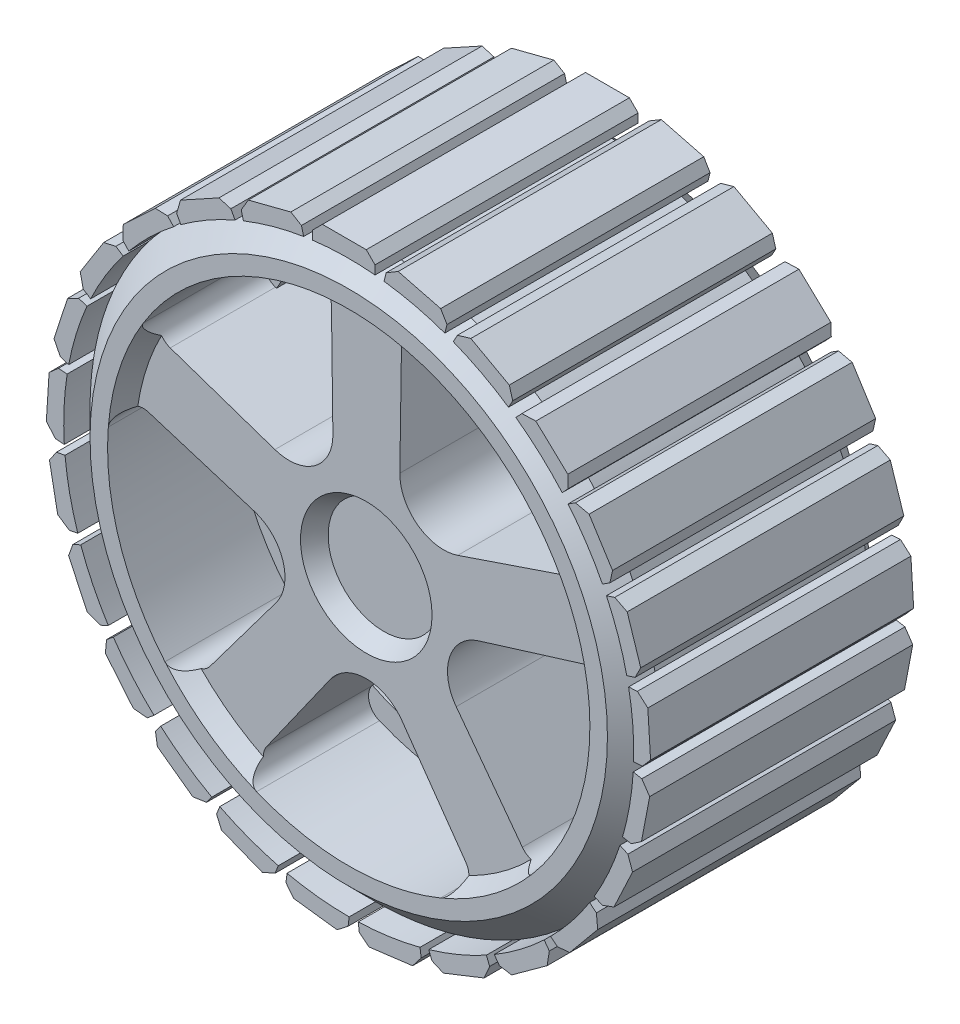
SolidWorks part; units mm, degrees
ref_plane "Front Plane" through (0, 0, 0) normal (0, 0, 1) x (1, 0, 0)
ref_plane "Top Plane" through (0, 0, 0) normal (0, 1, 0) x (1, 0, 0)
ref_plane "Right Plane" through (0, 0, 0) normal (1, 0, 0) x (0, 0, -1)
sketch "Sketch1" plane through (0, 0, 0) normal (0, 0, 1) x (1, 0, 0)
  circle A0 centre (0, 0) radius 32.5
  dimension "D1" = 65
extrude "Boss-Extrude1" add sketch "Sketch1" along normal mid plane 30
sketch "Sketch3" plane through (0, 0, 15) normal (0, 0, 1) x (1, 0, 0)
  line L0 (-24.6182, 12.2553) -> (-10.4207, 7.4109)
  line L1 (-3.8065, 12.2075) -> (-4, 27.2075)
  line L2 (0, 0) -> (0, 89.3086) construction
  line L3 (4.048, 27.2004) -> (3.828, 12.2008)
  line L4 (10.4338, 7.3925) -> (24.6398, 12.2118)
  line L5 (27.1201, 4.5555) -> (12.7866, 0.1296)
  line L6 (10.2549, -7.6387) -> (19.2283, -19.6602)
  line L7 (12.7131, -24.385) -> (4.0745, -12.1207)
  line L8 (-4.0959, -12.1135) -> (-12.7561, -24.3625)
  line L9 (-19.2629, -19.6262) -> (-10.2684, -7.6206)
  line L10 (-12.7863, 0.1522) -> (-27.112, 4.6034)
  circle A1 centre (0, 0) radius 27.5
  arc A2 (-10.4207, 7.4109) -> (-3.8065, 12.2075) centre (-8.8061, 12.143) ccw
  arc A3 (-4, 27.2075) -> (-24.6182, 12.2553) centre (0, 0) ccw
  circle A4 centre (0, 0) radius 10 construction
  arc A5 (24.6398, 12.2118) -> (4.048, 27.2004) centre (0, 0) ccw
  arc A6 (3.828, 12.2008) -> (10.4338, 7.3925) centre (8.8275, 12.1275) ccw
  arc A7 (19.2283, -19.6602) -> (27.1201, 4.5555) centre (0, 0) ccw
  arc A8 (12.7866, 0.1296) -> (10.2549, -7.6387) centre (14.2618, -4.6478) ccw
  arc A9 (-12.7561, -24.3625) -> (12.7131, -24.385) centre (0, 0) ccw
  arc A10 (4.0745, -12.1207) -> (-4.0959, -12.1135) centre (-0.0132, -15) ccw
  arc A11 (-27.112, 4.6034) -> (-19.2629, -19.6262) centre (0, 0) ccw
  arc A12 (-10.2684, -7.6206) -> (-12.7863, 0.1522) centre (-14.2699, -4.6227) ccw
  point P35 (0, 0)
  dimension "D1" = 55
  dimension "D2" = 5
  dimension "D6" = 20
  dimension "D3" = 15
  dimension "D4" = 8
  dimension "D5" = 5
extrude "Cut-Extrude1" cut sketch "Sketch3" against normal through all contours L0 A2 L1 A1 | L9 A12 L10 A1 | L7 A10 L8 A1 | L5 A8 L6 A1 | L3 A6 L4 A1
fillet "Fillet1" radius 2 10 edges at (4.048, 27.2004, 0) (24.6398, 12.2118, 0) (27.1201, 4.5555, 0) (19.2283, -19.6602, 0) (12.7131, -24.385, 0) (-12.7561, -24.3625, 0) (-19.2629, -19.6262, 0) (-27.112, 4.6034, 0) (-24.6182, 12.2553, 0) (-4, 27.2075, 0)
sketch "Sketch5" plane through (0, 0, 15) normal (0, 0, 1) x (1, 0, 0)
  circle A0 centre (0, 0) radius 27.5
  dimension "D1" = 55
extrude "Cut-Extrude2" cut sketch "Sketch5" against normal blind 2 draft 30
sketch "Sketch7" plane through (0, 0, 13) normal (0, 0, 1) x (1, 0, 0)
  circle A0 centre (0, 0) radius 7.5
  point P2 (0, 0)
  dimension "D1" = 15
extrude "Cut-Extrude3" cut sketch "Sketch7" against normal blind 2 draft 30
mirror "Mirror1" about plane through (0, 0, 0) normal (0, 0, 1) of "Cut-Extrude3", "Cut-Extrude2"
chamfer "Chamfer1" distance 3 angle 45 2 edges at (32.5, 0, -15) (32.5, 0, 15)
sketch "Sketch9" plane through (0, 0, 0) normal (0, 0, 1) x (1, 0, 0)
  circle A16 centre (0, 0) radius 25
  circle A17 centre (0, 0) radius 30
  dimension "D1" = 50
  dimension "D2" = 5
extrude "Boss-Extrude2" add sketch "Sketch9" along normal mid plane 2
sketch "Sketch10" plane through (0, 0, 0) normal (0, 0, 1) x (1, 0, 0)
  line L0 (-4.1239, 32.2373) -> (-4.1239, 33.2373)
  line L1 (-3, 34.3612) -> (2, 34.3612)
  line L2 (3, 33.3612) -> (3, 32.3612)
  line L3 (0, 0) -> (0, -50000) construction
  line L4 (3, 33.3612) -> (2, 34.3612)
  line L5 (-4.1239, 33.2373) -> (-3, 34.3612)
  line L6 (4.0227, 32.2501) -> (4.2714, 33.2187)
  line L7 (4.2714, 33.2187) -> (5.6395, 34.0278)
  line L8 (5.6395, 34.0278) -> (10.4825, 32.7843)
  line L9 (11.2024, 31.5671) -> (10.4825, 32.7843)
  line L10 (11.2024, 31.5671) -> (10.9537, 30.5985)
  line L11 (11.9166, 30.2365) -> (12.3983, 31.1128)
  line L12 (12.3983, 31.1128) -> (13.9247, 31.5562)
  line L13 (13.9247, 31.5562) -> (18.3063, 29.1475)
  line L14 (18.7008, 27.7894) -> (18.3063, 29.1475)
  line L15 (18.7008, 27.7894) -> (18.2191, 26.9131)
  line L16 (19.0617, 26.323) -> (19.7463, 27.052)
  line L17 (19.7463, 27.052) -> (21.335, 27.1019)
  line L18 (21.335, 27.1019) -> (24.9798, 23.6792)
  line L19 (25.0242, 22.2657) -> (24.9798, 23.6792)
  line L20 (25.0242, 22.2657) -> (24.3397, 21.5367)
  line L21 (25.0091, 20.7556) -> (25.8535, 21.2914)
  line L22 (25.8535, 21.2914) -> (27.4047, 20.9447)
  line L23 (27.4047, 20.9447) -> (30.0838, 16.723)
  line L24 (29.7753, 15.3429) -> (30.0838, 16.723)
  line L25 (29.7753, 15.3429) -> (28.931, 14.807)
  line L26 (29.3851, 13.884) -> (30.3362, 14.193)
  line L27 (30.3362, 14.193) -> (31.7524, 13.4714)
  line L28 (31.7524, 13.4714) -> (33.2975, 8.7161)
  line L29 (32.6555, 7.456) -> (33.2975, 8.7161)
  line L30 (32.6555, 7.456) -> (31.7044, 7.147)
  line L31 (31.9147, 6.14) -> (32.9128, 6.2028)
  line L32 (32.9128, 6.2028) -> (34.1051, 5.1516)
  line L33 (34.1051, 5.1516) -> (34.419, 0.1615)
  line L34 (33.4838, -0.8993) -> (34.419, 0.1615)
  line L35 (33.4838, -0.8993) -> (32.4858, -0.9621)
  line L36 (32.439, -1.9898) -> (33.4213, -2.1771)
  line L37 (33.4213, -2.1771) -> (34.3148, -3.4918)
  line L38 (34.3148, -3.4918) -> (33.3778, -8.4032)
  line L39 (32.2082, -9.1981) -> (33.3778, -8.4032)
  line L40 (32.2082, -9.1981) -> (31.2259, -9.0108)
  line L41 (30.9251, -9.9945) -> (31.8299, -10.4203)
  line L42 (31.8299, -10.4203) -> (32.3683, -11.9158)
  line L43 (32.3683, -11.9158) -> (30.2394, -16.44)
  line L44 (28.9088, -16.919) -> (30.2394, -16.44)
  line L45 (28.9088, -16.919) -> (28.004, -16.4932)
  line L46 (27.468, -17.3713) -> (28.2385, -18.0087)
  line L47 (28.2385, -18.0087) -> (28.3881, -19.5911)
  line L48 (28.3881, -19.5911) -> (25.2009, -23.4437)
  line L49 (23.793, -23.5768) -> (25.2009, -23.4437)
  line L50 (23.793, -23.5768) -> (23.0225, -22.9394)
  line L51 (22.285, -23.6565) -> (22.8727, -24.4655)
  line L52 (22.8727, -24.4655) -> (22.6241, -26.0355)
  line L53 (22.6241, -26.0355) -> (18.579, -28.9744)
  line L54 (17.1822, -28.7532) -> (18.579, -28.9744)
  line L55 (17.1822, -28.7532) -> (16.5944, -27.9442)
  line L56 (15.7017, -28.4553) -> (16.0698, -29.3851)
  line L57 (16.0698, -29.3851) -> (15.4385, -30.8439)
  line L58 (15.4385, -30.8439) -> (10.7897, -32.6845)
  line L59 (9.4918, -32.1229) -> (10.7897, -32.6845)
  line L60 (9.4918, -32.1229) -> (9.1236, -31.1931)
  line L61 (8.1318, -31.4662) -> (8.2572, -32.4583)
  line L62 (8.2572, -32.4583) -> (7.2829, -33.7143)
  line L63 (7.2829, -33.7143) -> (2.3224, -34.341)
  line L64 (1.2049, -33.4742) -> (2.3224, -34.341)
  line L65 (1.2049, -33.4742) -> (1.0796, -32.4821)
  line L66 (0.051, -32.5) -> (-0.0743, -33.4921)
  line L67 (-0.0743, -33.4921) -> (-1.3303, -34.4663)
  line L68 (-1.3303, -34.4663) -> (-6.2908, -33.8396)
  line L69 (-7.1576, -32.7222) -> (-6.2908, -33.8396)
  line L70 (-7.1576, -32.7222) -> (-7.0323, -31.7301)
  line L71 (-8.033, -31.4916) -> (-8.4011, -32.4214)
  line L72 (-8.4011, -32.4214) -> (-9.8599, -33.0526)
  line L73 (-9.8599, -33.0526) -> (-14.5088, -31.212)
  line L74 (-15.0704, -29.9141) -> (-14.5088, -31.212)
  line L75 (-15.0704, -29.9141) -> (-14.7023, -28.9843)
  line L76 (-15.6123, -28.5045) -> (-16.2, -29.3135)
  line L77 (-16.2, -29.3135) -> (-17.77, -29.5622)
  line L78 (-17.77, -29.5622) -> (-21.8151, -26.6233)
  line L79 (-22.0363, -25.2265) -> (-21.8151, -26.6233)
  line L80 (-22.0363, -25.2265) -> (-21.4485, -24.4174)
  line L81 (-22.2106, -23.7264) -> (-22.9811, -24.3638)
  line L82 (-22.9811, -24.3638) -> (-24.5635, -24.2142)
  line L83 (-24.5635, -24.2142) -> (-27.7506, -20.3617)
  line L84 (-27.6176, -18.9537) -> (-27.7506, -20.3617)
  line L85 (-27.6176, -18.9537) -> (-26.847, -18.3163)
  line L86 (-27.4133, -17.4574) -> (-28.3181, -17.8832)
  line L87 (-28.3181, -17.8832) -> (-29.8136, -17.3448)
  line L88 (-29.8136, -17.3448) -> (-31.9425, -12.8207)
  line L89 (-31.4635, -11.49) -> (-31.9425, -12.8207)
  line L90 (-31.4635, -11.49) -> (-30.5587, -11.0643)
  line L91 (-30.8935, -10.0916) -> (-31.8758, -10.279)
  line L92 (-31.8758, -10.279) -> (-33.1905, -9.3855)
  line L93 (-33.1905, -9.3855) -> (-34.1274, -4.4741)
  line L94 (-33.3325, -3.3044) -> (-34.1274, -4.4741)
  line L95 (-33.3325, -3.3044) -> (-32.3502, -3.117)
  line L96 (-32.4326, -2.0916) -> (-33.4307, -2.0288)
  line L97 (-33.4307, -2.0288) -> (-34.4818, -0.8365)
  line L98 (-34.4818, -0.8365) -> (-34.1679, 4.1536)
  line L99 (-33.107, 5.0888) -> (-34.1679, 4.1536)
  line L100 (-33.107, 5.0888) -> (-32.109, 5.0261)
  line L101 (-31.9339, 6.0398) -> (-32.8849, 6.3488)
  line L102 (-32.8849, 6.3488) -> (-33.6065, 7.765)
  line L103 (-33.6065, 7.765) -> (-32.0614, 12.5203)
  line L104 (-30.8014, 13.1624) -> (-32.0614, 12.5203)
  line L105 (-30.8014, 13.1624) -> (-29.8503, 12.8533)
  line L106 (-29.4286, 13.7916) -> (-30.2729, 14.3275)
  line L107 (-30.2729, 14.3275) -> (-30.6196, 15.8787)
  line L108 (-30.6196, 15.8787) -> (-27.9405, 20.1003)
  line L109 (-26.5603, 20.4088) -> (-27.9405, 20.1003)
  line L110 (-26.5603, 20.4088) -> (-25.716, 19.873)
  line L111 (-25.0742, 20.6769) -> (-25.7587, 21.4059)
  line L112 (-25.7587, 21.4059) -> (-25.7088, 22.9946)
  line L113 (-25.7088, 22.9946) -> (-22.064, 26.4174)
  line L114 (-20.6504, 26.3729) -> (-22.064, 26.4174)
  line L115 (-20.6504, 26.3729) -> (-19.9659, 25.644)
  line L116 (-19.1443, 26.263) -> (-19.626, 27.1393)
  line L117 (-19.626, 27.1393) -> (-19.1826, 28.6657)
  line L118 (-19.1826, 28.6657) -> (-14.801, 31.0745)
  line L119 (-13.443, 30.6799) -> (-14.801, 31.0745)
  line L120 (-13.443, 30.6799) -> (-12.9612, 29.8036)
  line L121 (-12.0115, 30.1989) -> (-12.2602, 31.1675)
  line L122 (-12.2602, 31.1675) -> (-11.451, 32.5357)
  line L123 (-11.451, 32.5357) -> (-6.6081, 33.7791)
  line L124 (-5.3909, 33.0592) -> (-6.6081, 33.7791)
  line L125 (-5.3909, 33.0592) -> (-5.1422, 32.0906)
  circle A0 centre (0, 0) radius 32.5 construction
  arc A1 (-4.1239, 32.2373) -> (3, 32.3612) centre (0, 0) cw
  arc A2 (4.0227, 32.2501) -> (10.9537, 30.5985) centre (0, 0) cw
  arc A3 (11.9166, 30.2365) -> (18.2191, 26.9131) centre (0, 0) cw
  arc A4 (19.0617, 26.323) -> (24.3397, 21.5367) centre (0, 0) cw
  arc A5 (25.0091, 20.7556) -> (28.931, 14.807) centre (0, 0) cw
  arc A6 (29.3851, 13.884) -> (31.7044, 7.147) centre (0, 0) cw
  arc A7 (31.9147, 6.14) -> (32.4858, -0.9621) centre (0, 0) cw
  arc A8 (32.439, -1.9898) -> (31.2259, -9.0108) centre (0, 0) cw
  arc A9 (30.9251, -9.9945) -> (28.004, -16.4932) centre (0, 0) cw
  arc A10 (27.468, -17.3713) -> (23.0225, -22.9394) centre (0, 0) cw
  arc A11 (22.285, -23.6565) -> (16.5944, -27.9442) centre (0, 0) cw
  arc A12 (15.7017, -28.4553) -> (9.1236, -31.1931) centre (0, 0) cw
  arc A13 (8.1318, -31.4662) -> (1.0796, -32.4821) centre (0, 0) cw
  arc A14 (0.051, -32.5) -> (-7.0323, -31.7301) centre (0, 0) cw
  arc A15 (-8.033, -31.4916) -> (-14.7023, -28.9843) centre (0, 0) cw
  arc A16 (-15.6123, -28.5045) -> (-21.4485, -24.4174) centre (0, 0) cw
  arc A17 (-22.2106, -23.7264) -> (-26.847, -18.3163) centre (0, 0) cw
  arc A18 (-27.4133, -17.4574) -> (-30.5587, -11.0643) centre (0, 0) cw
  arc A19 (-30.8935, -10.0916) -> (-32.3502, -3.117) centre (0, 0) cw
  arc A20 (-32.4326, -2.0916) -> (-32.109, 5.0261) centre (0, 0) cw
  arc A21 (-31.9339, 6.0398) -> (-29.8503, 12.8533) centre (0, 0) cw
  arc A22 (-29.4286, 13.7916) -> (-25.716, 19.873) centre (0, 0) cw
  arc A23 (-25.0742, 20.6769) -> (-19.9659, 25.644) centre (0, 0) cw
  arc A24 (-19.1443, 26.263) -> (-12.9612, 29.8036) centre (0, 0) cw
  arc A25 (-12.0115, 30.1989) -> (-5.1422, 32.0906) centre (0, 0) cw
  point P158 (0, 0)
  dimension "D1" = 2
  dimension "D2" = 3
  dimension "D3" = 1
  dimension "D4" = 45
  dimension "D5" = 45
  dimension "D6" = 1
  dimension "D7" = 6
  dimension "D8" = 25
extrude "Boss-Extrude3" add sketch "Sketch10" along normal mid plane 30
sketch "Sketch11" plane through (0, 0, -11) normal (0, 0, -1) x (-1, 0, 0)
  circle A0 centre (0, 0) radius 5
  dimension "D1" = 10
extrude "Boss-Extrude4" add sketch "Sketch11" along normal blind 4
sketch "Sketch12" plane through (0, 0, -15) normal (0, 0, -1) x (-1, 0, 0)
  circle A0 centre (0, 0) radius 3
  dimension "D1" = 6
extrude "Cut-Extrude4" cut sketch "Sketch12" against normal blind 10
